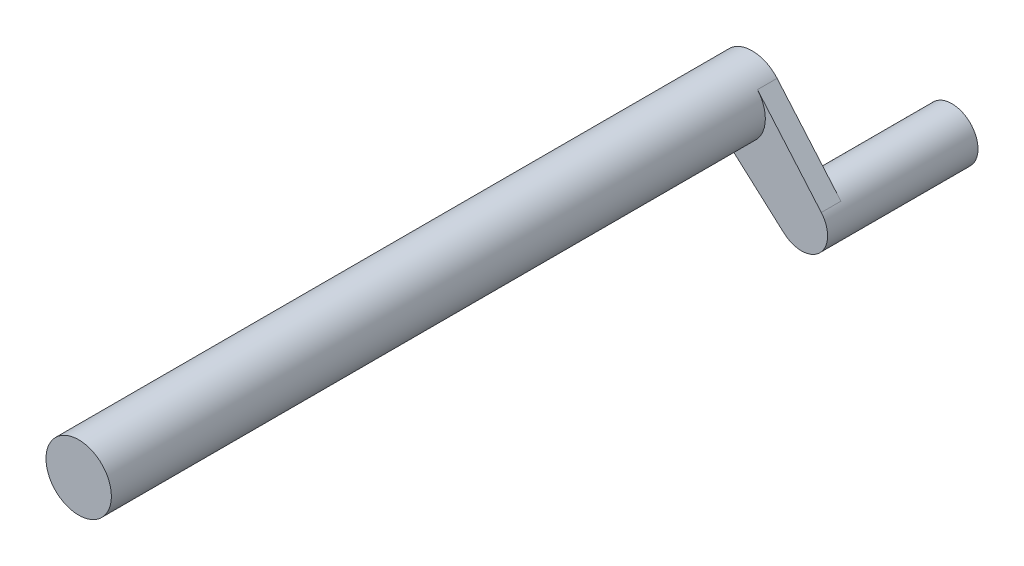
SolidWorks part; units mm, degrees
ref_plane "Front Plane" through (0, 0, 0) normal (0, 0, 1) x (1, 0, 0)
ref_plane "Top Plane" through (0, 0, 0) normal (0, 1, 0) x (1, 0, 0)
ref_plane "Right Plane" through (0, 0, 0) normal (1, 0, 0) x (0, 0, -1)
sketch "Sketch1" plane through (0, 0, 0) normal (0, 0, 1) x (1, 0, 0)
  circle A0 centre (0, 0) radius 10
  dimension "D1" = 20
extrude "Boss-Extrude1" add sketch "Sketch1" along normal blind 200
cosmetic thread "Cosmetic Thread1" parameters "D1"=100, "D2"=17.252
cosmetic thread "Cosmetic Thread2" parameters "D1"=150, "D2"=17.252
sketch "Sketch2" plane through (0, 0, 0) normal (0, 0, -1) x (-1, 0, 0)
  line L0 (-27.1176, -16.2677) -> (-7.5921, 6.5085)
  line L1 (-15.7152, -27.4415) -> (6.6609, -7.4587)
  arc A0 (6.6609, -7.4587) -> (-7.5921, 6.5085) centre (0, 0) ccw
  arc A1 (-27.1176, -16.2677) -> (-15.7152, -27.4415) centre (-21.0439, -21.4745) ccw
  dimension "D1" = 8
  dimension "D2" = 30
extrude "Boss-Extrude2" add sketch "Sketch2" along normal blind 6
sketch "Sketch4" plane through (0, 0, -6) normal (0, 0, -1) x (-1, 0, 0)
  circle A0 centre (-21.0439, -21.4745) radius 8
extrude "Boss-Extrude3" add sketch "Sketch4" along normal blind 40
